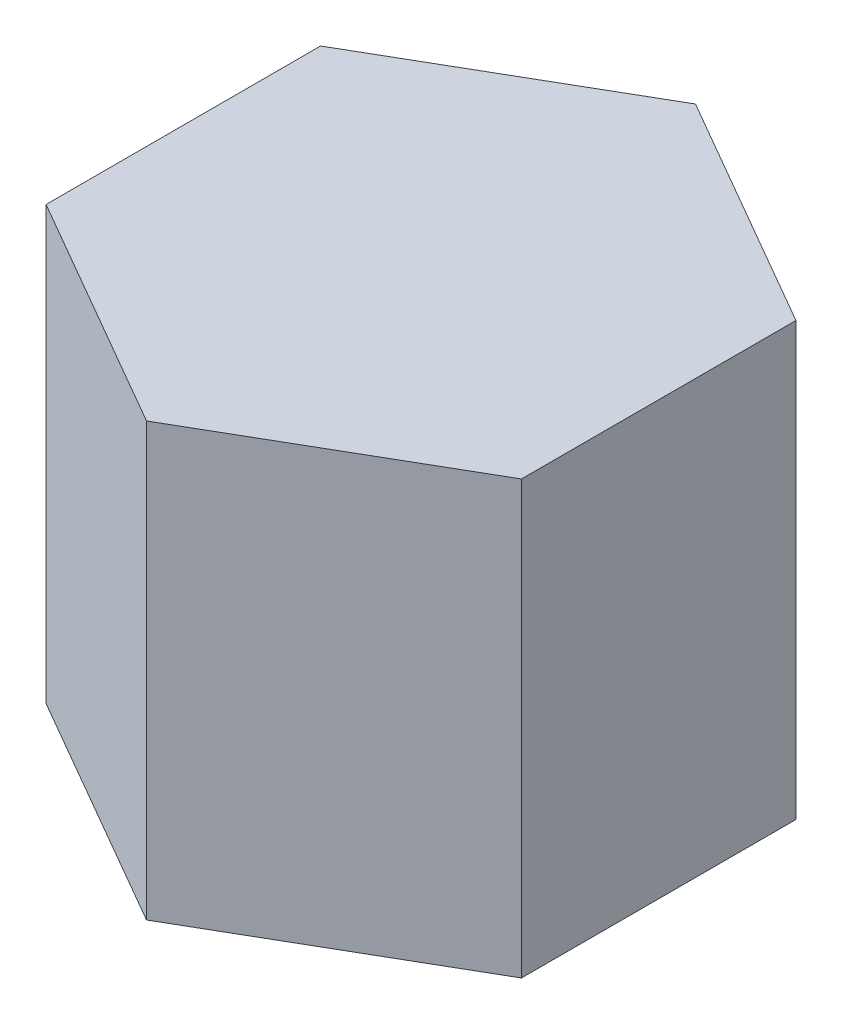
SolidWorks part; units mm, degrees
ref_plane "Front Plane" through (0, 0, 0) normal (0, 0, 1) x (1, 0, 0)
ref_plane "Top Plane" through (0, 0, 0) normal (0, 1, 0) x (1, 0, 0)
ref_plane "Right Plane" through (0, 0, 0) normal (1, 0, 0) x (0, 0, -1)
sketch "Sketch1" plane through (0, 0, 0) normal (0, 1, 0) x (1, 0, 0)
  line L1 (0, 12.7017) -> (-11, 6.3509)
  line L2 (-11, 6.3509) -> (-11, -6.3509)
  line L3 (-11, -6.3509) -> (0, -12.7017)
  line L4 (0, -12.7017) -> (11, -6.3509)
  line L5 (11, -6.3509) -> (11, 6.3509)
  line L6 (11, 6.3509) -> (0, 12.7017)
  circle A0 centre (0, 0) radius 11 construction
  dimension "D1" = 22
extrude "Boss-Extrude1" add sketch "Sketch1" along normal blind 20
